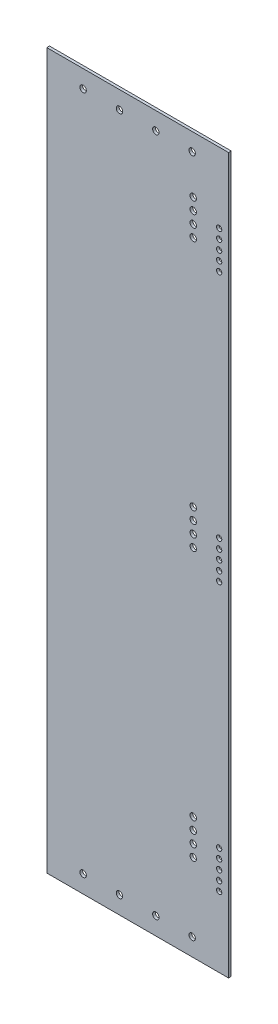
SolidWorks part; units mm, degrees
material "5052-H32"
ref_plane "Front Plane" through (0, 0, 0) normal (0, 0, 1) x (1, 0, 0)
ref_plane "Top Plane" through (0, 0, 0) normal (0, 1, 0) x (1, 0, 0)
ref_plane "Right Plane" through (0, 0, 0) normal (1, 0, 0) x (0, 0, -1)
sketch "Sketch1" plane through (0, 0, 0) normal (0, 0, 1) x (1, 0, 0)
  line L0 (55, 0) -> (-55, 0) construction
  line L1 (-77.5, 304.8) -> (77.5, 304.8)
  line L2 (-77.5, 304.8) -> (-77.5, -304.8)
  line L3 (-77.5, -304.8) -> (77.5, -304.8)
  line L4 (77.5, 304.8) -> (77.5, -304.8)
  line L5 (-77.5, 304.8) -> (77.5, -304.8) construction
  line L6 (-77.5, -304.8) -> (77.5, 304.8) construction
  point P0 (0, 0)
  point P5 (69.5, 244.8)
  point P7 (69.5, 228.8)
  point P8 (69.5, 236.8)
  point P9 (69.5, 220.8)
  point P10 (69.5, 212.8)
  point P11 (69.5, 8)
  point P12 (69.5, 16)
  point P13 (69.5, -212.8)
  point P14 (69.5, -228.8)
  point P15 (69.5, -220.8)
  point P16 (69.5, -236.8)
  point P17 (69.5, -244.8)
  point P18 (69.5, -8)
  point P19 (69.5, -16)
  point P20 (-46.5, 289.795)
  point P21 (-15.5, 289.795)
  point P22 (69.5, 0)
  point P23 (15.5, 289.795)
  point P24 (46.5, 289.795)
  point P29 (46.5, -289.795)
  point P30 (15.5, -289.795)
  point P31 (-15.5, -289.795)
  point P32 (-46.5, -289.795)
  point P33 (47.4, 226.8)
  point P34 (47.4, 236.8)
  point P35 (47.4, 246.8)
  point P36 (47.4, 256.8)
  point P37 (47.4, 8)
  point P38 (47.4, 18)
  point P39 (47.4, -2)
  point P40 (47.4, 28)
  point P41 (47.4, -220.8)
  point P42 (47.4, -210.8)
  point P43 (47.4, -230.8)
  point P44 (47.4, -200.8)
  point P45 (0, 0)
  dimension "D1" = 609.6
  dimension "D2" = 155
  dimension "D3" = 8
  dimension "D4" = 60
  dimension "D5" = 8
  dimension "D6" = 8
  dimension "D7" = 8
  dimension "D8" = 8
  dimension "D9" = 60
  dimension "D10" = 8
  dimension "D11" = 8
  dimension "D12" = 8
  dimension "D13" = 8
  dimension "D14" = 8
  dimension "D15" = 8
  dimension "D16" = 8
  dimension "D17" = 8
  dimension "D18" = 8
  dimension "D19" = 8
  dimension "D20" = 31
  dimension "D21" = 31
  dimension "D22" = 31
  dimension "D23" = 31
  dimension "D24" = 15.005
  dimension "D29" = 10
  dimension "D30" = 10
  dimension "D31" = 10
  dimension "D32" = 22.1
  dimension "D33" = 10
  dimension "D34" = 10
  dimension "D35" = 10
  dimension "D36" = 22.1
  dimension "D37" = 10
  dimension "D38" = 10
  dimension "D39" = 10
  dimension "D40" = 22.1
extrude "Boss-Extrude1" add sketch "Sketch1" along normal blind 2.305
hole_wizard "M4 Clearance Hole1" positions "Sketch3" profile "Sketch5" hole size "M4" standard "ANSI Metric" end condition through all
sketch "Sketch3" plane through (0, 0, 2.305) normal (0, 0, 1) x (1, 0, 0)
  point P4 (69.5, 228.8)
  point P9 (69.5, 244.8)
  point P12 (69.5, 236.8)
  point P15 (69.5, 220.8)
  point P18 (69.5, 212.8)
  point P21 (69.5, 16)
  point P24 (69.5, 8)
  point P27 (69.5, 0)
  point P30 (69.5, -8)
  point P33 (69.5, -16)
  point P36 (69.5, -212.8)
  point P39 (69.5, -220.8)
  point P42 (69.5, -228.8)
  point P45 (69.5, -236.8)
  point P48 (69.5, -244.8)
sketch "Sketch5" plane through (69.5, 228.8, 2.305) normal (1, 0, 0) x (0, -1, 0)
  line L0 (0, 0) -> (0, 2.305)
  line L1 (0, 2.305) -> (2.25, 2.305)
  line L2 (2.25, 2.305) -> (2.25, 0)
  line L5 (2.25, 0) -> (0, 0)
  line L11 (0, -6.35) -> (0, 107.95) construction
  dimension "Thru Hole Dia." = 4.5
  dimension "Thru Hole Depth" = 2.305
hole_wizard "M5 Clearance Hole1" positions "Sketch6" profile "Sketch7" hole size "M5" standard "ANSI Metric" end condition through all
sketch "Sketch6" plane through (0, 0, 2.305) normal (0, 0, 1) x (1, 0, 0)
  point P0 (-46.5, -289.795)
  point P3 (-15.5, -289.795)
  point P6 (15.5, -289.795)
  point P9 (46.5, -289.795)
  point P12 (-46.5, 289.795)
  point P15 (-15.5, 289.795)
  point P18 (15.5, 289.795)
  point P21 (46.5, 289.795)
  point P24 (47.4, -230.8)
  point P27 (47.4, -220.8)
  point P30 (47.4, -210.8)
  point P33 (47.4, -200.8)
  point P36 (47.4, -2)
  point P39 (47.4, 8)
  point P42 (47.4, 18)
  point P45 (47.4, 28)
  point P48 (47.4, 226.8)
  point P51 (47.4, 236.8)
  point P54 (47.4, 246.8)
  point P57 (47.4, 256.8)
sketch "Sketch7" plane through (-46.5, -289.795, 2.305) normal (1, 0, 0) x (0, -1, 0)
  line L0 (0, 0) -> (0, 2.305)
  line L1 (0, 2.305) -> (2.75, 2.305)
  line L2 (2.75, 2.305) -> (2.75, 0)
  line L5 (2.75, 0) -> (0, 0)
  line L11 (0, -6.35) -> (0, 107.95) construction
  dimension "Thru Hole Dia." = 5.5
  dimension "Thru Hole Depth" = 2.305
